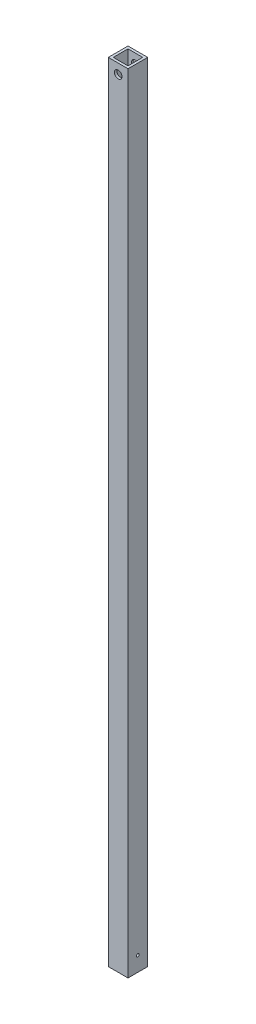
SolidWorks part; units mm, degrees
material "1060 Alloy"
ref_plane "Front Plane" through (0, 0, 0) normal (0, 0, 1) x (1, 0, 0)
ref_plane "Top Plane" through (0, 0, 0) normal (0, 1, 0) x (1, 0, 0)
ref_plane "Right Plane" through (0, 0, 0) normal (1, 0, 0) x (0, 0, -1)
sketch "Sketch1" plane through (0, 0, 0) normal (0, 1, 0) x (1, 0, 0)
  line L1 (-6.35, 6.35) -> (6.35, 6.35)
  line L2 (-6.35, 6.35) -> (-6.35, -6.35)
  line L3 (-6.35, -6.35) -> (6.35, -6.35)
  line L4 (6.35, 6.35) -> (6.35, -6.35)
  line L5 (-6.35, 6.35) -> (6.35, -6.35) construction
  line L6 (-6.35, -6.35) -> (6.35, 6.35) construction
  point P0 (0, 0)
  dimension "D1" = 12.7
extrude "Extrude-Thin1" add sketch "Sketch1" along normal blind 508 thin
sketch "Sketch3" plane through (0, 0, 6.35) normal (0, 0, 1) x (1, 0, 0)
  line L0 (-6.35, 508) -> (6.35, 508) construction
  line L1 (6.35, 508) -> (6.35, 0) construction
  circle A0 centre (0, 501.65) radius 2.4765
  dimension "D1" = 4.953
  dimension "D2" = 6.35
  dimension "D3" = 6.35
extrude "Cut-Extrude2" cut sketch "Sketch3" against normal through all and the other way through all
sketch "Sketch4" plane through (6.35, 0, 0) normal (1, 0, 0) x (0, 0, -1)
  line L0 (-6.35, 0) -> (6.35, 0) construction
  circle A0 centre (0, 9.525) radius 0.889
  dimension "D1" = 1.778
  dimension "D2" = 9.525
extrude "Cut-Extrude3" cut sketch "Sketch4" against normal up to next contours A0
sketch "Sketch5" plane through (-6.35, 0, 0) normal (-1, 0, 0) x (0, 0, 1)
  line L0 (-6.35, 0) -> (6.35, 0) construction
  line L1 (-3.175, 0) -> (3.175, 0)
  line L2 (-3.175, 0) -> (-3.175, 9.525)
  line L3 (-3.175, 9.525) -> (3.175, 9.525)
  line L4 (3.175, 0) -> (3.175, 9.525)
  line L5 (-6.35, 508) -> (-6.35, 0) construction
  dimension "D1" = 6.35
  dimension "D2" = 9.525
  dimension "D3" = 3.175
extrude "Cut-Extrude4" [suppressed] cut sketch "Sketch5" against normal up to next
